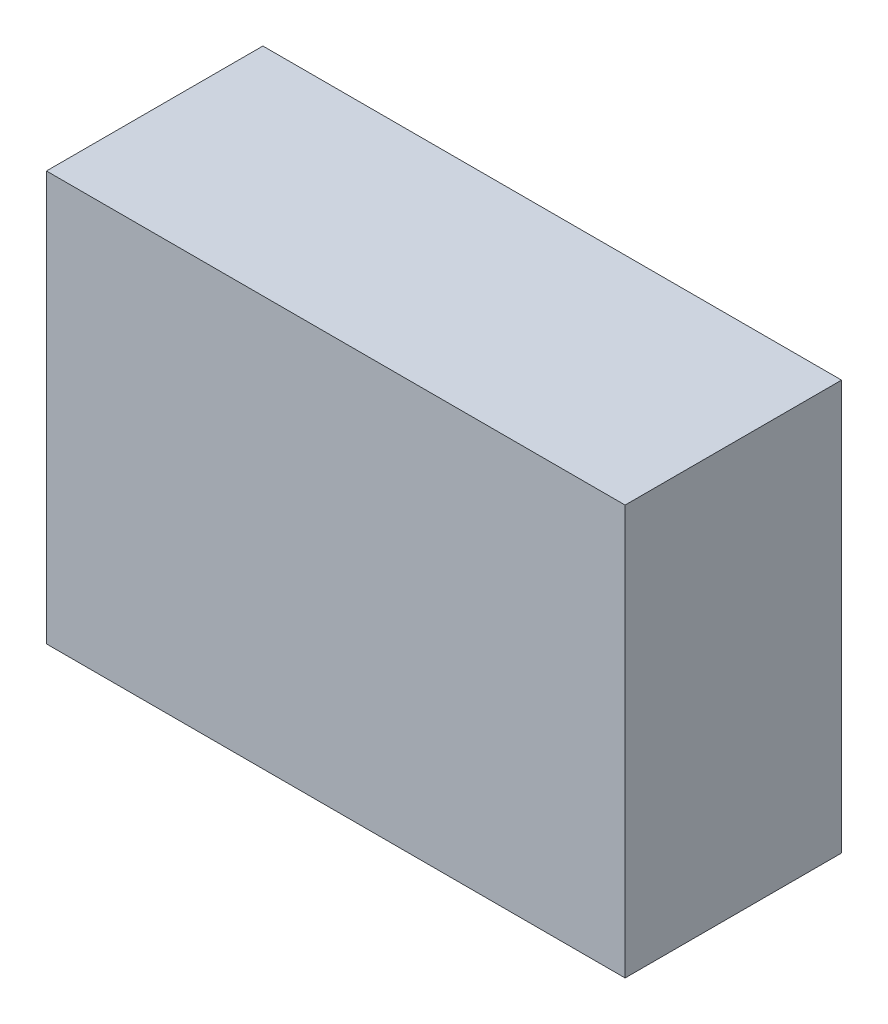
SolidWorks part; units mm, degrees
ref_plane "Plano frontal" through (0, 0, 0) normal (0, 0, 1) x (1, 0, 0)
ref_plane "Plano superior" through (0, 0, 0) normal (0, 1, 0) x (1, 0, 0)
ref_plane "Plano direito" through (0, 0, 0) normal (1, 0, 0) x (0, 0, -1)
sketch "Esboço1" plane through (0, 0, 0) normal (0, 0, 1) x (1, 0, 0)
  line L1 (0, 0) -> (770, 0)
  line L2 (0, 0) -> (0, 545)
  line L3 (0, 545) -> (770, 545)
  line L4 (770, 0) -> (770, 545)
  dimension "D1" = 770
  dimension "D2" = 545
extrude "Ressalto-extrusão1" add sketch "Esboço1" along normal blind 288
